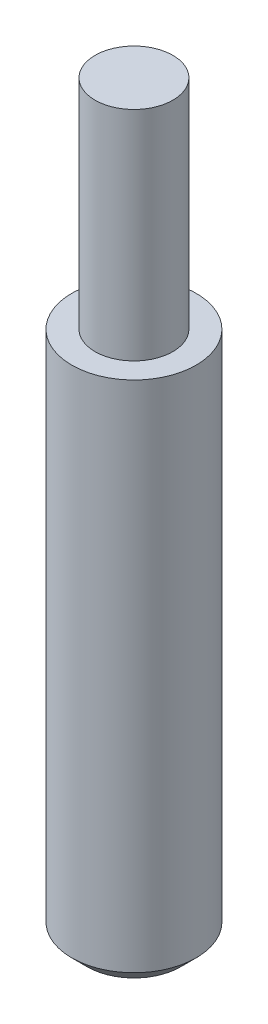
SolidWorks part; units mm, degrees
ref_plane "Front Plane" through (0, 0, 0) normal (0, 0, 1) x (1, 0, 0)
ref_plane "Top Plane" through (0, 0, 0) normal (0, 1, 0) x (1, 0, 0)
ref_plane "Right Plane" through (0, 0, 0) normal (1, 0, 0) x (0, 0, -1)
sketch "Sketch1" plane through (0, 0, 0) normal (0, 1, 0) x (1, 0, 0)
  circle A0 centre (0, 0) radius 101.6
  dimension "D1" = 203.2
extrude "Boss-Extrude1" add sketch "Sketch1" along normal blind 1219.2
sketch "Sketch2" plane through (0, 1219.2, 0) normal (0, 1, 0) x (1, 0, 0)
  circle A0 centre (0, 0) radius 63.5
  dimension "D1" = 127
extrude "Cut-Extrude1" cut sketch "Sketch2" against normal blind 355.6 flip side to cut
chamfer "Chamfer1" distance 25.4 angle 45 1 edges at (0, 0, 101.6)
